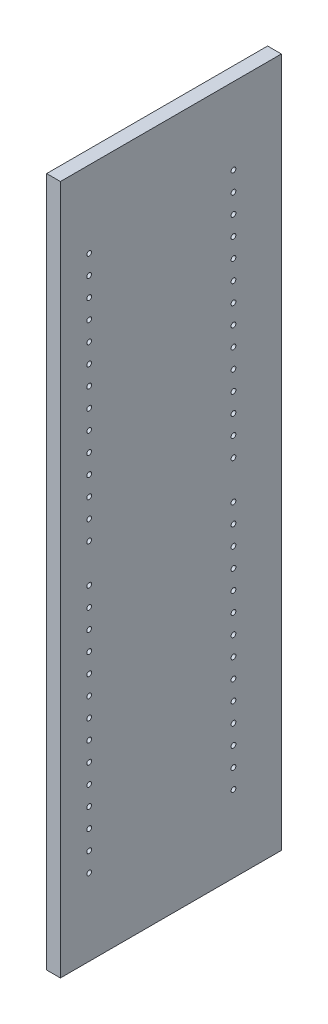
SolidWorks part; units mm, degrees
material "Cedar"
ref_plane "Front Plane" through (0, 0, 0) normal (0, 0, 1) x (1, 0, 0)
ref_plane "Top Plane" through (0, 0, 0) normal (0, 1, 0) x (1, 0, 0)
ref_plane "Right Plane" through (0, 0, 0) normal (1, 0, 0) x (0, 0, -1)
sketch "Sketch1" plane through (0, 0, 0) normal (1, 0, 0) x (0, 0, -1)
  line L1 (-146.4469, -457.2) -> (146.4469, -457.2)
  line L2 (-146.4469, -457.2) -> (-146.4469, 457.2)
  line L3 (-146.4469, 457.2) -> (146.4469, 457.2)
  line L4 (146.4469, -457.2) -> (146.4469, 457.2)
  line L5 (-146.4469, -457.2) -> (146.4469, 457.2) construction
  line L6 (-146.4469, 457.2) -> (146.4469, -457.2) construction
  point P0 (0, 0)
  dimension "D1" = 292.8938
  dimension "D2" = 914.4
extrude "Boss-Extrude1" add sketch "Sketch1" along normal blind 18.2562
sketch "Sketch3" plane through (18.2562, 0, 0) normal (1, 0, 0) x (0, 0, -1)
  line L0 (-108.3469, 457.2) -> (-108.3469, -457.2) construction
  line L1 (146.4469, 457.2) -> (-146.4469, 457.2) construction
  line L2 (-146.4469, -457.2) -> (146.4469, -457.2) construction
  line L3 (-12.7, 457.2) -> (-12.7, -457.2) construction
  line L4 (-146.4469, 457.2) -> (-146.4469, -457.2) construction
  line L5 (0, 0) -> (-12.7, 0) construction
  line L6 (-12.7, 0) -> (-108.3469, 0) construction
  circle A0 centre (-108.3469, 355.6) radius 3.175
  circle A1 centre (-108.3469, 330.2) radius 3.175
  circle A2 centre (-108.3469, 304.8) radius 3.175
  circle A3 centre (-108.3469, 279.4) radius 3.175
  circle A4 centre (-108.3469, 254) radius 3.175
  circle A5 centre (-108.3469, 228.6) radius 3.175
  circle A6 centre (-108.3469, 203.2) radius 3.175
  circle A7 centre (-108.3469, 177.8) radius 3.175
  circle A8 centre (-108.3469, 152.4) radius 3.175
  circle A9 centre (-108.3469, 127) radius 3.175
  circle A10 centre (-108.3469, 101.6) radius 3.175
  circle A11 centre (-108.3469, 76.2) radius 3.175
  circle A24 centre (-108.3469, 50.8) radius 3.175
  circle A25 centre (-108.3469, 25.4) radius 3.175
  circle A26 centre (82.9469, 25.4) radius 3.175
  circle A27 centre (82.9469, 50.8) radius 3.175
  circle A28 centre (82.9469, 76.2) radius 3.175
  circle A29 centre (82.9469, 101.6) radius 3.175
  circle A30 centre (82.9469, 127) radius 3.175
  circle A31 centre (82.9469, 152.4) radius 3.175
  circle A32 centre (82.9469, 177.8) radius 3.175
  circle A33 centre (82.9469, 203.2) radius 3.175
  circle A34 centre (82.9469, 228.6) radius 3.175
  circle A35 centre (82.9469, 254) radius 3.175
  circle A36 centre (82.9469, 279.4) radius 3.175
  circle A37 centre (82.9469, 304.8) radius 3.175
  circle A38 centre (82.9469, 330.2) radius 3.175
  circle A39 centre (82.9469, 355.6) radius 3.175
  circle A40 centre (82.9469, -355.6) radius 3.175
  circle A41 centre (82.9469, -330.2) radius 3.175
  circle A42 centre (82.9469, -304.8) radius 3.175
  circle A43 centre (82.9469, -279.4) radius 3.175
  circle A44 centre (82.9469, -254) radius 3.175
  circle A45 centre (82.9469, -228.6) radius 3.175
  circle A46 centre (82.9469, -203.2) radius 3.175
  circle A47 centre (82.9469, -177.8) radius 3.175
  circle A48 centre (82.9469, -152.4) radius 3.175
  circle A49 centre (82.9469, -127) radius 3.175
  circle A50 centre (82.9469, -101.6) radius 3.175
  circle A51 centre (82.9469, -76.2) radius 3.175
  circle A52 centre (82.9469, -50.8) radius 3.175
  circle A53 centre (82.9469, -25.4) radius 3.175
  circle A54 centre (-108.3469, -25.4) radius 3.175
  circle A55 centre (-108.3469, -50.8) radius 3.175
  circle A56 centre (-108.3469, -76.2) radius 3.175
  circle A57 centre (-108.3469, -101.6) radius 3.175
  circle A58 centre (-108.3469, -127) radius 3.175
  circle A59 centre (-108.3469, -152.4) radius 3.175
  circle A60 centre (-108.3469, -177.8) radius 3.175
  circle A61 centre (-108.3469, -203.2) radius 3.175
  circle A62 centre (-108.3469, -228.6) radius 3.175
  circle A63 centre (-108.3469, -254) radius 3.175
  circle A64 centre (-108.3469, -279.4) radius 3.175
  circle A65 centre (-108.3469, -304.8) radius 3.175
  circle A66 centre (-108.3469, -330.2) radius 3.175
  circle A67 centre (-108.3469, -355.6) radius 3.175
  dimension "D1" = 6.35
  dimension "D2" = 38.1
  dimension "D3" = 101.6
  dimension "D5" = 25.4
  dimension "D6" = 12.7
  dimension "D4" = 14
extrude "Cut-Extrude1" cut sketch "Sketch3" against normal blind 9.525
